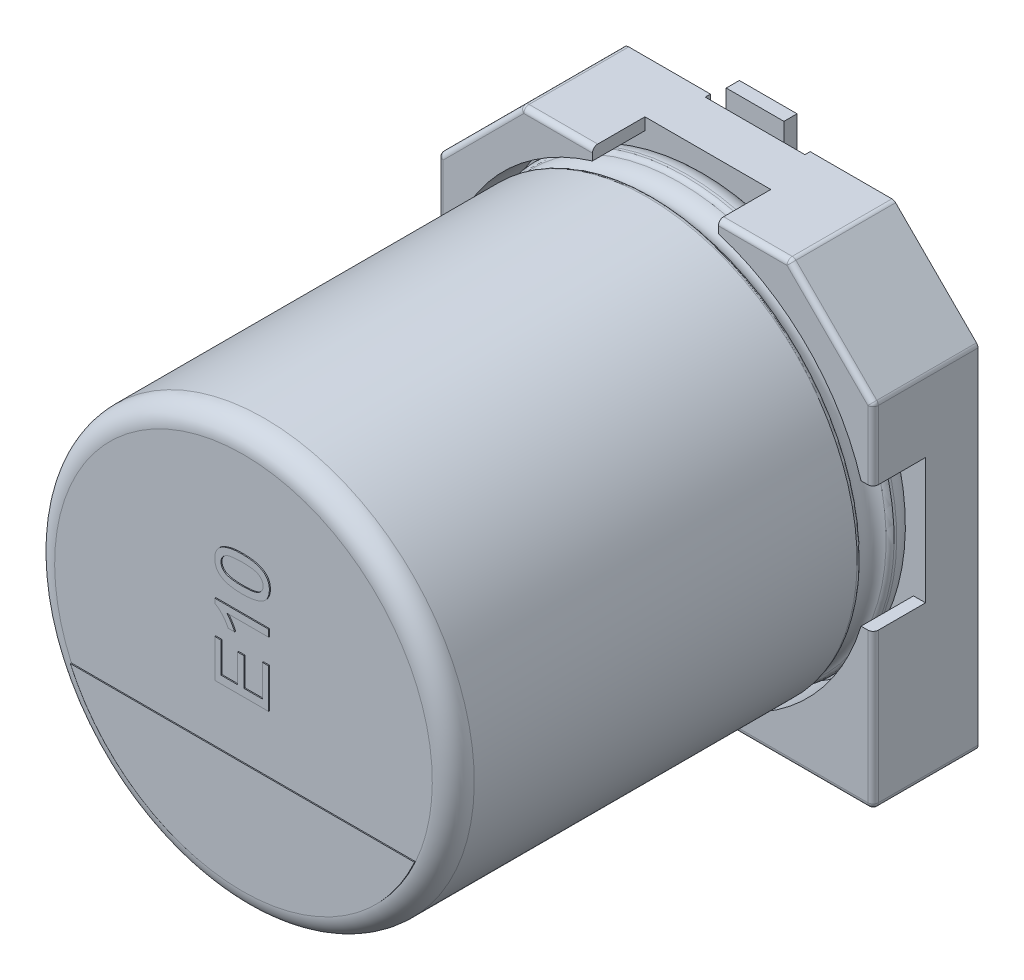
SolidWorks part; units mm, degrees
ref_plane "Plan de face" through (0, 0, 0) normal (0, 0, 1) x (1, 0, 0)
ref_plane "Plan de dessus" through (0, 0, 0) normal (0, 1, 0) x (1, 0, 0)
ref_plane "Plan de droite" through (0, 0, 0) normal (1, 0, 0) x (0, 0, -1)
sketch "Sketch2" plane through (0, 0, 0) normal (0, 0, 1) x (1, 0, 0)
  line L0 (-4.15, 2.55) -> (-2.55, 4.15)
  line L1 (-2.55, 4.15) -> (2.55, 4.15)
  line L2 (-4.15, 2.55) -> (-4.15, -4.15)
  line L3 (-4.15, -4.15) -> (4.15, -4.15)
  line L4 (4.15, 2.55) -> (4.15, -4.15)
  line L5 (-4.15, 4.15) -> (4.15, -4.15) construction
  line L6 (-4.15, -4.15) -> (4.15, 4.15) construction
  line L7 (2.55, 4.15) -> (4.15, 2.55)
  point P0 (0, 0)
  dimension "D1" = 8.3
  dimension "D2" = 8.3
extrude "Boss-Extrude1" add sketch "Sketch2" along normal blind 1
sketch "Sketch4" plane through (0, 0, 1) normal (0, 0, 1) x (1, 0, 0)
  line L0 (-4.15, 2.55) -> (-2.55, 4.15)
  line L1 (-2.55, 4.15) -> (-1.2, 4.15)
  line L3 (-4.15, 1.2) -> (-4.15, 2.55)
  line L4 (2.55, 4.15) -> (4.15, 2.55)
  line L5 (4.15, 2.55) -> (4.15, 1.2)
  line L6 (4.15, -4.15) -> (4.15, 2.55) construction
  line L7 (2.55, 4.15) -> (-2.55, 4.15) construction
  line L8 (1.2, 4.15) -> (2.55, 4.15)
  line L9 (-4.15, -4.15) -> (4.15, -4.15) construction
  line L10 (4.15, -1.2) -> (4.15, -4.15)
  line L11 (4.15, -4.15) -> (1.2, -4.15)
  line L12 (-4.15, -1.2) -> (-4.15, -4.15)
  line L13 (-4.15, -4.15) -> (-1.2, -4.15)
  line L14 (-4.946, -1.2) -> (4.946, -1.2) construction
  line L15 (-4.8253, 1.2) -> (5.0249, 1.2) construction
  line L16 (3.9205, 1.2) -> (4.15, 1.2)
  line L17 (3.9205, -1.2) -> (4.15, -1.2)
  line L18 (-3.9205, -1.2) -> (-4.15, -1.2)
  line L19 (-3.9205, 1.2) -> (-4.15, 1.2)
  line L20 (-1.2, 5.0139) -> (-1.2, -5.2906) construction
  line L21 (1.2, 5.0139) -> (1.2, -5.4) construction
  line L22 (-1.2, 4.15) -> (-1.2, 3.9205)
  line L23 (1.2, 4.15) -> (1.2, 3.9205)
  line L24 (-1.2, -3.9205) -> (-1.2, -4.15)
  line L25 (1.2, -3.9205) -> (1.2, -4.15)
  arc A0 (-1.2, 3.9205) -> (-3.9205, 1.2) centre (0, 0) ccw construction
  arc A1 (-3.9205, 1.2) -> (-1.2, 3.9205) centre (0, 0) cw
  arc A2 (1.2, 3.9205) -> (3.9205, 1.2) centre (0, 0) cw
  arc A3 (1.2, -3.9205) -> (3.9205, -1.2) centre (0, 0) ccw
  arc A4 (-1.2, -3.9205) -> (-3.9205, -1.2) centre (0, 0) cw
  arc A5 (3.9205, 1.2) -> (1.2, 3.9205) centre (0, 0) ccw construction
  arc A6 (1.2, -3.9205) -> (3.9205, -1.2) centre (0, 0) ccw construction
  arc A7 (-3.9205, -1.2) -> (-1.2, -3.9205) centre (0, 0) ccw construction
  point P33 (0, -1.2)
  dimension "D1" = 8.2
  dimension "D2" = 1.2
  dimension "D3" = 1.2
  dimension "D4" = 1.2
  dimension "D5" = 1.2
sketch "Sketch5" plane through (0, 0, 0) normal (0, 0, 1) x (1, 0, 0)
extrude "Boss-Extrude2" add sketch "Sketch4" along normal blind 1
sketch "Sketch7" plane through (0, 0, 0) normal (0, 0, -1) x (1, 0, 0)
  line L1 (-2.9065, 2.8449) -> (2.9065, 2.8449) construction
  line L2 (-2.9065, 2.8449) -> (-2.9065, -2.8449) construction
  line L3 (-2.9065, -2.8449) -> (2.9065, -2.8449) construction
  line L4 (2.9065, 2.8449) -> (2.9065, -2.8449) construction
  line L5 (-2.9065, 2.8449) -> (2.9065, -2.8449) construction
  line L6 (-2.9065, -2.8449) -> (2.9065, 2.8449) construction
  circle A0 centre (-2.9065, 2.8449) radius 0.35
  circle A1 centre (2.9065, 2.8449) radius 0.35
  circle A2 centre (-2.9065, -2.8449) radius 0.35
  circle A3 centre (2.9065, -2.8449) radius 0.35
  point P0 (0, 0)
  dimension "D1" = 0.7
  dimension "D2" = 0.7
  dimension "D3" = 0.7
  dimension "D4" = 0.7
extrude "Spacer Pad" add sketch "Sketch7" along normal blind 0.15
sketch "Sketch8" plane through (0, 0, 0) normal (0, 0, -1) x (1, 0, 0)
  line L0 (-0.95, 4.3618) -> (-0.95, -4.4479) construction
  line L1 (0.95, 4.3618) -> (0.95, -4.4479) construction
  dimension "D1" = 0.95
  dimension "D2" = 1.9
sketch "Sketch9" plane through (0, 0, 0) normal (0, 0, -1) x (1, 0, 0)
  line L0 (-4.6239, -1.5) -> (5.0007, -1.5) construction
  line L1 (-4.6239, 1.5) -> (5.2975, 1.5) construction
  line L2 (-0.95, 4.3618) -> (-0.95, -4.4479) construction
  line L3 (-0.95, 1.5) -> (0.95, 1.5)
  line L4 (-0.95, 1.5) -> (-0.95, 4.15)
  line L5 (-0.95, 4.15) -> (0.95, 4.15)
  line L6 (0.95, 1.5) -> (0.95, 4.15)
  line L7 (0.95, 4.3618) -> (0.95, -4.4479) construction
  line L8 (-4.15, 4.15) -> (4.15, 4.15) construction
  line L9 (2.55, -4.15) -> (-2.55, -4.15) construction
  line L10 (-0.95, -1.5) -> (0.95, -1.5)
  line L11 (-0.95, -1.5) -> (-0.95, -4.15)
  line L12 (-0.95, -4.15) -> (0.95, -4.15)
  line L13 (0.95, -1.5) -> (0.95, -4.15)
  dimension "D1" = 1.5
  dimension "D2" = 1.5
extrude "Cut-Extrude1" cut sketch "Sketch9" against normal blind 0.1
fillet "Fillet1" radius 0.1 6 edges at (-4.15, 2.55, 1) (-2.55, 4.15, 1) (2.55, 4.15, 1) (4.15, 2.55, 1) (4.15, -4.15, 1) (-4.15, -4.15, 1)
sketch "Sketch10" plane through (0, 0, 0) normal (1, 0, 0) x (0, 0, -1)
  line L0 (18.9631, 0) -> (-18.9631, 0) construction
  line L2 (-9.8536, 0) -> (-9.8536, 3.6)
  line L3 (-9.4536, 4) -> (-2.1546, 4)
  line L4 (-1, 3.6) -> (-1, 0)
  line L7 (-1.4494, 4) -> (-1.4, 4)
  arc A0 (-9.8536, 3.6) -> (-9.4536, 4) centre (-9.4536, 3.6) cw
  arc A1 (-1.4, 4) -> (-1, 3.6) centre (-1.4, 3.6) cw
  arc A2 (-1.5413, 3.9394) -> (-2.0626, 3.9394) centre (-1.802, 4.051) cw
  arc A3 (-2.0626, 3.9394) -> (-2.1546, 4) centre (-2.1546, 3.9) ccw
  arc A4 (-1.5413, 3.9394) -> (-1.4494, 4) centre (-1.4494, 3.9) cw
  point P4 (0, 0)
  point P13 (-9.8536, 4)
  dimension "D2" = 0.4
  dimension "D3" = 0.4
  dimension "D4" = 0.1
  dimension "D5" = 0.1
  dimension "D1" = 4
revolve "Revolve1" add sketch "Sketch10" angle 360 about L0
fillet "Fillet2" radius 0.1 16 edges at (2.625, -4.15, 2) (4.1207, -4.1207, 2) (4.15, 1.8543, 2) (4.1424, 2.5468, 2) (1.8543, 4.15, 2) (2.5468, 4.1424, 2) (-1.8543, 4.15, 2) (-2.5468, 4.1424, 2) (-3.35, 3.35, 2) (-4.1424, 2.5468, 2) (-4.15, -2.625, 2) (-4.1207, -4.1207, 2) (4.15, -2.625, 2) (3.35, 3.35, 2) (-4.15, 1.8543, 2) (-2.625, -4.15, 2)
sketch "Sketch13" plane through (0, 0, 9.8536) normal (0, 0, 1) x (1, 0, 0)
  line L0 (-5.2631, -1.4818) -> (3.7173, -1.4818) construction
  line L1 (-3.2809, -1.4818) -> (3.2809, -1.4818)
  arc A0 (3.2809, -1.4818) -> (-3.2809, -1.4818) centre (0, 0) cw
  point P3 (-0.7729, -1.4818)
extrude "Cathode marker" add sketch "Sketch13" along normal blind 0.02
sketch "Sketch15" plane through (0, 0, 9.8536) normal (0, 0, 1) x (1, 0, 0)
  line L1 (0.5, 2.1812) -> (0.5, -0.5) construction
  text T1 "E10" font "Arial" height in points 4
extrude "Text" add sketch "Sketch15" along normal blind 0.02
sketch "Sketch18" plane through (0, 0, 0.1) normal (0, 0, -1) x (1, 0, 0)
  line L0 (0, 5.1012) -> (0, -5.1012) construction
  point P4 (0, 0)
sketch "Sketch19" plane through (0, 0, 0.1) normal (0, 0, -1) x (1, 0, 0)
  line L0 (-1.0534, -4.5) -> (1.0534, -4.5) construction
  line L2 (-0.95, -4.15) -> (0.95, -4.15) construction
  line L3 (-1.9391, 4.5) -> (1.9391, 4.5) construction
  line L5 (0.95, 4.15) -> (-0.95, 4.15) construction
  line L6 (0, 5.1012) -> (0, -5.1012) construction
  line L7 (-0.55, 1.6) -> (0.55, 1.6)
  line L8 (-0.55, 1.6) -> (-0.55, 4.5)
  line L9 (-0.55, 4.5) -> (0.55, 4.5)
  line L10 (0.55, 1.6) -> (0.55, 4.5)
  line L11 (-0.55, 1.6) -> (0.55, 4.5) construction
  line L12 (-0.55, 4.5) -> (0.55, 1.6) construction
  line L14 (-0.55, -1.6) -> (0.55, -1.6)
  line L15 (-0.55, -1.6) -> (-0.55, -4.5)
  line L16 (-0.55, -4.5) -> (0.55, -4.5)
  line L17 (0.55, -1.6) -> (0.55, -4.5)
  line L18 (-0.55, -1.6) -> (0.55, -4.5) construction
  line L19 (-0.55, -4.5) -> (0.55, -1.6) construction
  point P3 (0, -4.5)
  point P8 (0, 4.5)
  point P10 (0, 3.05)
  point P17 (0, -3.05)
  dimension "D1" = 0.35
  dimension "D2" = 0.35
  dimension "D3" = 1.1
  dimension "D4" = 2.9
  dimension "D5" = 1.1
  dimension "D6" = 2.9
extrude "Boss-Extrude6" add sketch "Sketch19" along normal blind 0.25
